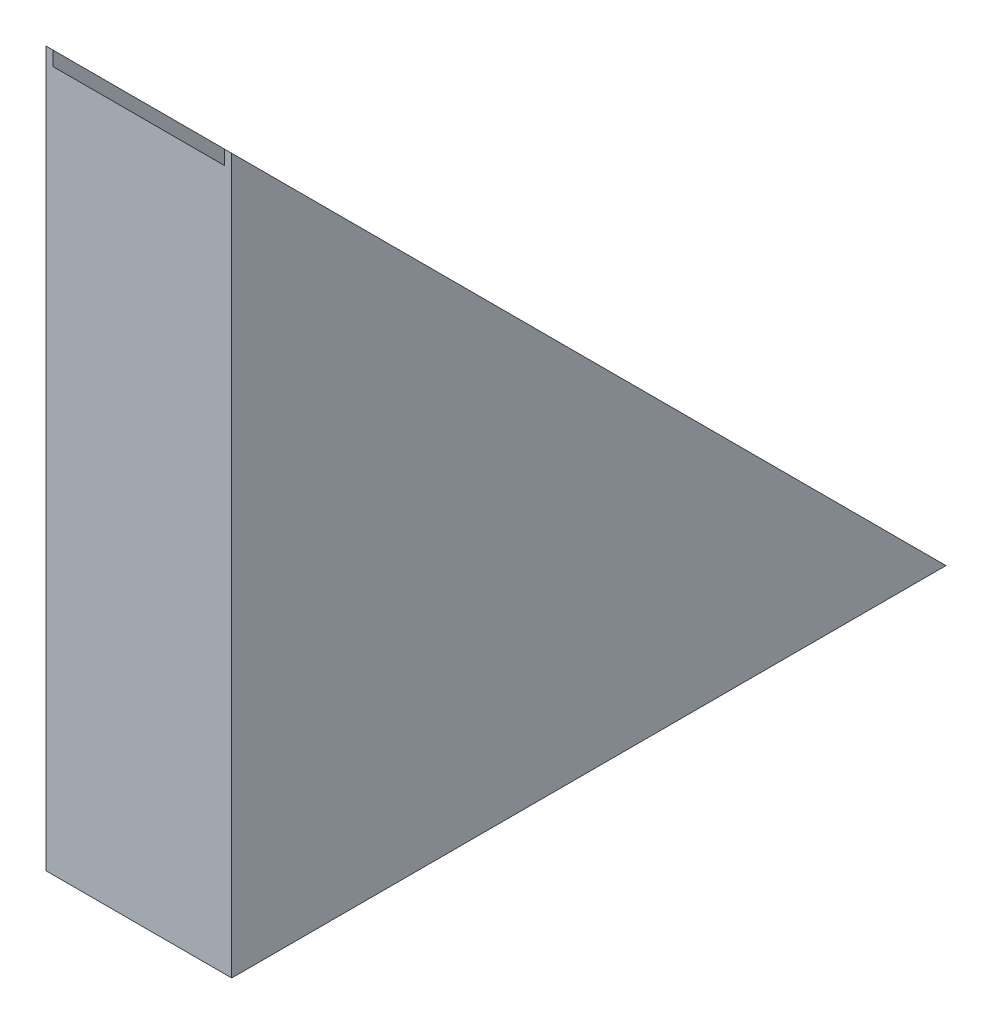
SolidWorks part; units mm, degrees
ref_plane "Front Plane" through (0, 0, 0) normal (0, 0, 1) x (1, 0, 0)
ref_plane "Top Plane" through (0, 0, 0) normal (0, 1, 0) x (1, 0, 0)
ref_plane "Right Plane" through (0, 0, 0) normal (1, 0, 0) x (0, 0, -1)
sketch "Sketch3" plane through (0, 0, 0) normal (1, 0, 0) x (0, 0, -1)
  line L0 (0, 0) -> (2500, 0)
  line L1 (0, 0) -> (0, 2500)
  line L2 (0, 2500) -> (2500, 0)
  dimension "D1" = 2500
  dimension "D2" = 2500
extrude "Boss-Extrude1" add sketch "Sketch3" along normal blind 650
sketch "Sketch5" plane through (0, 1250, -1250) normal (0, 0.7071, -0.7071) x (1, 0, 0)
  line L1 (650, -1767.767) -> (0, -1767.767) construction
  line L3 (650, 1767.767) -> (0, 1767.767) construction
  line L5 (625, 1767.767) -> (25, 1767.767)
  line L6 (625, 1767.767) -> (625, -1767.767)
  line L7 (625, -1767.767) -> (25, -1767.767)
  line L8 (25, 1767.767) -> (25, -1767.767)
extrude "Cut-Extrude1" cut sketch "Sketch5" against normal blind 35.36
